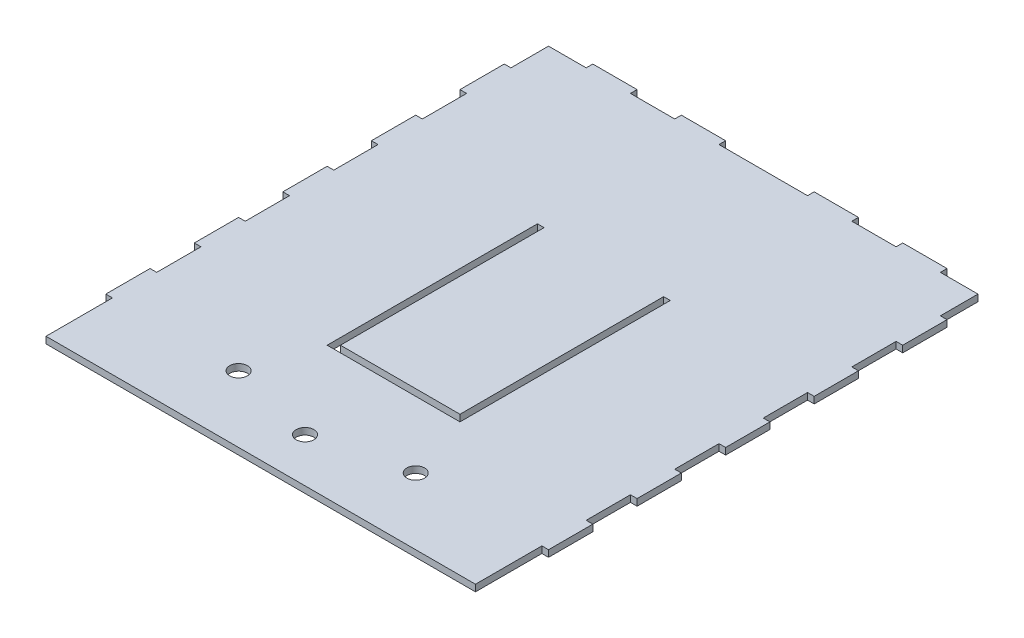
SolidWorks part; units mm, degrees
ref_plane "Front Plane" through (0, 0, 0) normal (0, 0, 1) x (1, 0, 0)
ref_plane "Top Plane" through (0, 0, 0) normal (0, 1, 0) x (1, 0, 0)
ref_plane "Right Plane" through (0, 0, 0) normal (1, 0, 0) x (0, 0, -1)
sketch "Sketch1" plane through (0, 0, 0) normal (0, 1, 0) x (1, 0, 0)
  line L0 (100, 90) -> (-100, 90)
  line L1 (100, -140) -> (-100, -140)
  line L2 (100, -140) -> (100, 90)
  line L4 (-100, -140) -> (-100, 90)
  line L5 (100, -100) -> (-90, 90) construction
  line L6 (90, 90) -> (-100, -100) construction
  point P0 (0, 0)
  point P6 (0, 0)
extrude "Boss-Extrude1" add sketch "Sketch1" along normal blind 3
sketch "Sketch2" plane through (0, 3, 0) normal (0, 1, 0) x (1, 0, 0)
  line L0 (-30, -80) -> (30, -80)
  line L1 (27, 20) -> (27, -77)
  line L2 (-30, 20) -> (-30, -80)
  line L3 (-27, -77) -> (27, -77)
  line L4 (30, 20) -> (30, -80)
  line L5 (-27, 20) -> (-27, -77)
  line L7 (-30, 20) -> (-27, 20)
  line L8 (27, 17) -> (27, -77) construction
  line L9 (-27, 17) -> (-27, -77) construction
  line L10 (-27, 17) -> (27, 17) construction
  line L11 (27, 20) -> (30, 20)
  line L12 (-30, 20) -> (30, 20) construction
  point P0 (0, 0)
extrude "Cut-Extrude2" cut sketch "Sketch2" against normal blind 3
sketch "Sketch5" plane through (0, 3, 0) normal (0, 1, 0) x (1, 0, 0)
  line L4 (100, -140) -> (100, 90)
  line L5 (100, 90) -> (-100, 90)
  line L6 (-100, 90) -> (-100, -140)
  line L7 (-100, -140) -> (100, -140)
  line L8 (100, -130) -> (100, -110)
  line L9 (100, 90) -> (80, 90)
  line L10 (-100, 90) -> (-100, 70)
  line L12 (100, 70) -> (97, 70)
  line L13 (100, 50) -> (97, 50)
  line L14 (100, 30) -> (97, 30)
  line L15 (100, 10) -> (97, 10)
  line L16 (97, -137) -> (97, 87)
  line L17 (97, 87) -> (-97, 87)
  line L18 (-97, 87) -> (-97, -137)
  line L19 (-97, -137) -> (97, -137)
  line L20 (97, -130) -> (97, -110)
  line L21 (97, 87) -> (80, 87)
  line L22 (-97, 87) -> (-97, 70)
  line L24 (100, -10) -> (97, -10)
  line L25 (100, -30) -> (97, -30)
  line L26 (100, -50) -> (97, -50)
  line L27 (100, -70) -> (97, -70)
  line L28 (100, -90) -> (97, -90)
  line L29 (100, -110) -> (97, -110)
  line L30 (100, -130) -> (97, -130)
  line L31 (-97, 70) -> (-100, 70)
  line L32 (-97, 50) -> (-100, 50)
  line L33 (-97, 30) -> (-100, 30)
  line L34 (-97, 10) -> (-100, 10)
  line L35 (-97, -10) -> (-100, -10)
  line L36 (-97, -30) -> (-100, -30)
  line L37 (-97, -50) -> (-100, -50)
  line L38 (-97, -70) -> (-100, -70)
  line L39 (-97, -90) -> (-100, -90)
  line L40 (-97, -110) -> (-100, -110)
  line L41 (-97, -130) -> (-100, -130)
  line L51 (80, 87) -> (80, 90)
  line L52 (60, 87) -> (60, 90)
  line L53 (40, 87) -> (40, 90)
  line L54 (20, 87) -> (20, 90)
  line L56 (-20, 87) -> (-20, 90)
  line L57 (-40, 87) -> (-40, 90)
  line L58 (-60, 87) -> (-60, 90)
  line L59 (-80, 87) -> (-80, 90)
  line L60 (100, 70) -> (100, 90)
  line L61 (97, 70) -> (97, 87)
  line L62 (-97, 50) -> (-97, 30)
  line L63 (-100, 50) -> (-100, 30)
  line L64 (97, 30) -> (97, 50)
  line L65 (100, 30) -> (100, 50)
  line L66 (-97, 10) -> (-97, -10)
  line L67 (-100, 10) -> (-100, -10)
  line L68 (100, -10) -> (100, 10)
  line L69 (97, -10) -> (97, 10)
  line L70 (-97, -30) -> (-97, -50)
  line L71 (-100, -30) -> (-100, -50)
  line L72 (100, -50) -> (100, -30)
  line L73 (97, -50) -> (97, -30)
  line L74 (-97, -70) -> (-97, -90)
  line L75 (-100, -70) -> (-100, -90)
  line L76 (100, -90) -> (100, -70)
  line L77 (97, -90) -> (97, -70)
  line L78 (-97, -110) -> (-97, -130)
  line L79 (-100, -110) -> (-100, -130)
  line L80 (60, 87) -> (40, 87)
  line L81 (60, 90) -> (40, 90)
  line L82 (-80, 87) -> (-97, 87)
  line L83 (-80, 90) -> (-100, 90)
  line L84 (-40, 87) -> (-60, 87)
  line L85 (-40, 90) -> (-60, 90)
  line L86 (20, 87) -> (-20, 87)
  line L87 (20, 90) -> (-20, 90)
  dimension "D1" = 0
  dimension "D2" = 3
  dimension "D3" = 12
extrude "Cut-Extrude4" cut sketch "Sketch5" against normal blind 3
sketch "Sketch6" plane through (0, 3, 0) normal (0, 1, 0) x (1, 0, 0)
  line L0 (27, 20) -> (27, -77) construction
  line L1 (30, 20) -> (27, 20)
  line L2 (30, 20) -> (30, 15)
  line L3 (30, 15) -> (27, 15)
  line L4 (27, 20) -> (27, 15)
  line L5 (-30, 20) -> (-30, -80) construction
  line L6 (-27, 20) -> (-30, 20)
  line L7 (-27, 20) -> (-27, 15)
  line L8 (-27, 15) -> (-30, 15)
  line L9 (-30, 20) -> (-30, 15)
extrude "Boss-Extrude2" add sketch "Sketch6" against normal blind 3
sketch "Sketch7" plane through (0, 3, 0) normal (0, 1, 0) x (1, 0, 0)
  line L1 (100, -140) -> (97, -140)
  line L2 (100, -140) -> (100, -130)
  line L3 (100, -130) -> (97, -130)
  line L4 (97, -140) -> (97, -130)
  line L5 (-100, -140) -> (-97, -140)
  line L6 (-100, -140) -> (-100, -130)
  line L7 (-100, -130) -> (-97, -130)
  line L8 (-97, -140) -> (-97, -130)
extrude "Cut-Extrude5" cut sketch "Sketch7" against normal blind 3
sketch "Sketch8" plane through (0, 3, 0) normal (0, 1, 0) x (1, 0, 0)
  circle A0 centre (0, -120) radius 4
  circle A1 centre (40, -110) radius 4
  circle A2 centre (-40, -110) radius 4
extrude "Cut-Extrude6" cut sketch "Sketch8" against normal blind 3
